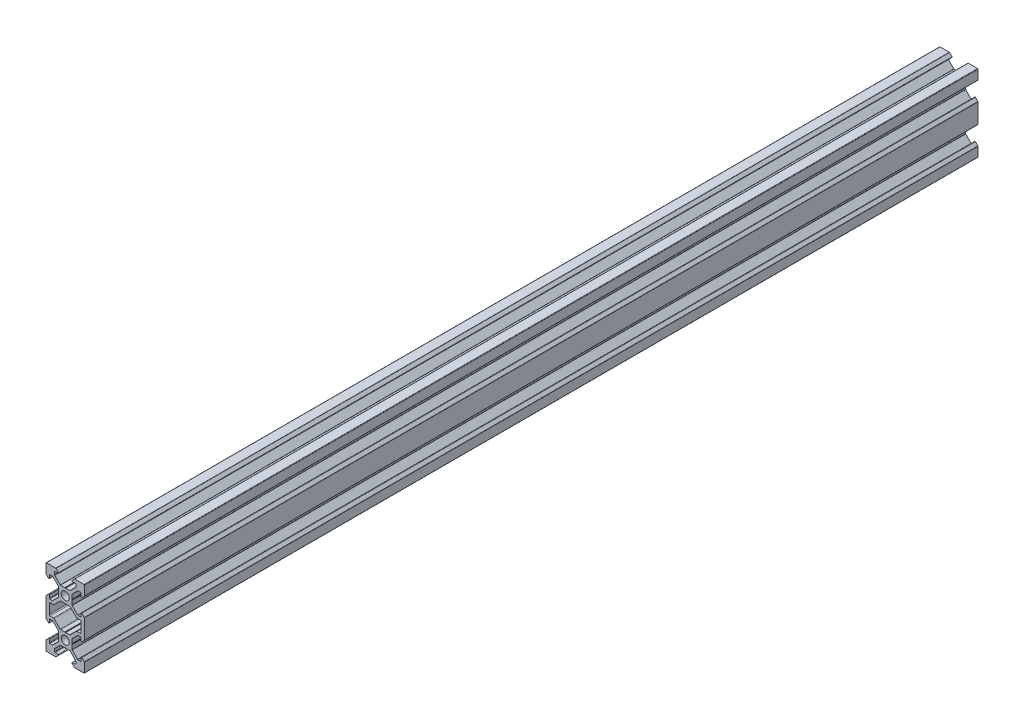
SolidWorks part; units mm, degrees
ref_plane "Front Plane" through (0, 0, 0) normal (0, 0, 1) x (1, 0, 0)
ref_plane "Top Plane" through (0, 0, 0) normal (0, 1, 0) x (1, 0, 0)
ref_plane "Right Plane" through (0, 0, 0) normal (1, 0, 0) x (0, 0, -1)
sketch "Sketch1" plane through (0, 0, 0) normal (0, 0, 1) x (1, 0, 0)
  line L0 (3.5607, 3.5607) -> (10.6317, 10.6317) construction
  line L1 (2.5, -3.5607) -> (-2.5, -3.5607)
  line L2 (3.5607, -2.5) -> (3.5607, 2.5)
  line L3 (2.5, 3.5607) -> (-2.5, 3.5607)
  line L4 (-3.5607, -2.5) -> (-3.5607, 2.5)
  line L5 (3.5607, -3.5607) -> (-3.5607, 3.5607) construction
  line L6 (3.5607, 3.5607) -> (-3.5607, -3.5607) construction
  line L7 (2.5, 3.5607) -> (5.5, 6.5607)
  line L8 (5.5, 6.5607) -> (5.5, 8.2521)
  line L9 (5.5, 8.2521) -> (3.1, 8.2521)
  line L10 (3.1, 8.2521) -> (4.8479, 10)
  line L11 (4.8479, 10) -> (10, 10)
  line L12 (3.5607, 2.5) -> (6.5607, 5.5)
  line L13 (6.5607, 5.5) -> (8.2521, 5.5)
  line L14 (8.2521, 5.5) -> (8.2521, 3.1)
  line L15 (8.2521, 3.1) -> (10, 4.8479)
  line L16 (10, 4.8479) -> (10, 10)
  line L17 (0, -55) -> (0, 55) construction
  line L18 (-3.5607, 3.5607) -> (-10.6317, 10.6317) construction
  line L19 (-10, 4.8479) -> (-10, 10)
  line L20 (-8.2521, 3.1) -> (-10, 4.8479)
  line L21 (-8.2521, 5.5) -> (-8.2521, 3.1)
  line L22 (-6.5607, 5.5) -> (-8.2521, 5.5)
  line L23 (-3.5607, 2.5) -> (-6.5607, 5.5)
  line L24 (-4.8479, 10) -> (-10, 10)
  line L25 (-3.1, 8.2521) -> (-4.8479, 10)
  line L26 (-5.5, 8.2521) -> (-3.1, 8.2521)
  line L27 (-5.5, 6.5607) -> (-5.5, 8.2521)
  line L28 (-2.5, 3.5607) -> (-5.5, 6.5607)
  line L29 (-8.2521, -7) -> (-5.9393, -7)
  line L30 (55, 0) -> (-55, 0) construction
  line L31 (-3.5607, -3.5607) -> (-10.6317, -10.6317) construction
  line L32 (3.5607, -3.5607) -> (10.6317, -10.6317) construction
  line L33 (-2.5, -3.5607) -> (-5.5, -6.5607)
  line L34 (-5.5, -6.5607) -> (-5.9393, -7)
  line L35 (5.5, -6.5607) -> (5.9393, -7)
  line L36 (8.2521, -7) -> (5.9393, -7)
  line L37 (-12.2633, -10) -> (14.5346, -10) construction
  line L38 (-3.5607, -2.5) -> (-6.5607, -5.5)
  line L39 (-6.5607, -5.5) -> (-8.2521, -5.5)
  line L40 (-8.2521, -5.5) -> (-8.2521, -3.1)
  line L41 (-8.2521, -3.1) -> (-10, -4.8479)
  line L42 (-10, -4.8479) -> (-10, -7)
  line L43 (10, -4.8479) -> (10, -7)
  line L44 (8.2521, -3.1) -> (10, -4.8479)
  line L45 (8.2521, -5.5) -> (8.2521, -3.1)
  line L46 (6.5607, -5.5) -> (8.2521, -5.5)
  line L47 (3.5607, -2.5) -> (6.5607, -5.5)
  line L48 (-3.5607, -23.5607) -> (-10.6317, -30.6317) construction
  line L49 (3.5607, -23.5607) -> (-3.5607, -16.4393) construction
  line L50 (3.5607, -16.4393) -> (-3.5607, -23.5607) construction
  line L51 (3.5607, -23.5607) -> (10.6317, -30.6317) construction
  line L52 (2.5, -3.5607) -> (5.5, -6.5607)
  line L53 (2.5, -16.4393) -> (5.5, -13.4393)
  line L54 (3.5607, -17.5) -> (6.5607, -14.5)
  line L55 (6.5607, -14.5) -> (8.2521, -14.5)
  line L56 (8.2521, -14.5) -> (8.2521, -16.9)
  line L57 (8.2521, -16.9) -> (10, -15.1521)
  line L58 (10, -15.1521) -> (10, -13)
  line L59 (-10, -15.1521) -> (-10, -13)
  line L60 (-8.2521, -16.9) -> (-10, -15.1521)
  line L61 (-8.2521, -14.5) -> (-8.2521, -16.9)
  line L62 (-6.5607, -14.5) -> (-8.2521, -14.5)
  line L63 (-3.5607, -17.5) -> (-6.5607, -14.5)
  line L64 (8.2521, -13) -> (5.9393, -13)
  line L65 (5.5, -13.4393) -> (5.9393, -13)
  line L66 (-5.5, -13.4393) -> (-5.9393, -13)
  line L67 (-2.5, -16.4393) -> (-5.5, -13.4393)
  line L68 (-8.2521, -13) -> (-5.9393, -13)
  line L69 (-2.5, -23.5607) -> (-5.5, -26.5607)
  line L70 (-5.5, -26.5607) -> (-5.5, -28.2521)
  line L71 (-5.5, -28.2521) -> (-3.1, -28.2521)
  line L72 (-3.1, -28.2521) -> (-4.8479, -30)
  line L73 (-4.8479, -30) -> (-10, -30)
  line L74 (-3.5607, -22.5) -> (-6.5607, -25.5)
  line L75 (-6.5607, -25.5) -> (-8.2521, -25.5)
  line L76 (-8.2521, -25.5) -> (-8.2521, -23.1)
  line L77 (-8.2521, -23.1) -> (-10, -24.8479)
  line L78 (-10, -24.8479) -> (-10, -30)
  line L79 (10, -24.8479) -> (10, -30)
  line L80 (8.2521, -23.1) -> (10, -24.8479)
  line L81 (8.2521, -25.5) -> (8.2521, -23.1)
  line L82 (6.5607, -25.5) -> (8.2521, -25.5)
  line L83 (3.5607, -22.5) -> (6.5607, -25.5)
  line L84 (4.8479, -30) -> (10, -30)
  line L85 (3.1, -28.2521) -> (4.8479, -30)
  line L86 (5.5, -28.2521) -> (3.1, -28.2521)
  line L87 (5.5, -26.5607) -> (5.5, -28.2521)
  line L88 (2.5, -23.5607) -> (5.5, -26.5607)
  line L89 (-3.5607, -17.5) -> (-3.5607, -22.5)
  line L90 (2.5, -23.5607) -> (-2.5, -23.5607)
  line L91 (3.5607, -17.5) -> (3.5607, -22.5)
  line L92 (2.5, -16.4393) -> (-2.5, -16.4393)
  line L93 (-10, -7) -> (-10, -13)
  line L94 (-8.2521, -13) -> (-8.2521, -7)
  line L95 (8.2521, -13) -> (8.2521, -7)
  line L96 (10, -7) -> (10, -13)
  circle A0 centre (0, 0) radius 2.1
  circle A1 centre (0, -20) radius 2.1
  point P0 (0, 0)
  point P102 (0, -20)
  dimension "D10" = 4.2
  dimension "D11" = 4.2
  dimension "D1" = 1.5
  dimension "D2" = 10
  dimension "D3" = 20
  dimension "D4" = 6.2
  dimension "D5" = 11
  dimension "D6" = 45
  dimension "D7" = 1.5
  dimension "D8" = 10
  dimension "D9" = 5
extrude "Boss-Extrude1" add sketch "Sketch1" along normal blind 465
fillet "Fillet1" radius 0.25 64 edges at (5.5, 6.5607, 232.5) (5.5, 8.2521, 232.5) (3.1, 8.2521, 232.5) (4.8479, 10, 232.5) (10, 10, 232.5) (10, 4.8479, 232.5) (8.2521, 3.1, 232.5) (8.2521, 5.5, 232.5) (6.5607, 5.5, 232.5) (3.5607, 2.5, 232.5) (3.5607, -2.5, 232.5) (6.5607, -5.5, 232.5) (8.2521, -5.5, 232.5) (8.2521, -3.1, 232.5) (10, -4.8479, 232.5) (10, -15.1521, 232.5) (8.2521, -16.9, 232.5) (8.2521, -14.5, 232.5) (6.5607, -14.5, 232.5) (3.5607, -17.5, 232.5) (3.5607, -22.5, 232.5) (6.5607, -25.5, 232.5) (8.2521, -25.5, 232.5) (8.2521, -23.1, 232.5) (10, -24.8479, 232.5) (10, -30, 232.5) (4.8479, -30, 232.5) (3.1, -28.2521, 232.5) (5.5, -28.2521, 232.5) (5.5, -26.5607, 232.5) (2.5, -23.5607, 232.5) (-2.5, -23.5607, 232.5) (-5.5, -26.5607, 232.5) (-5.5, -28.2521, 232.5) (-3.1, -28.2521, 232.5) (-4.8479, -30, 232.5) (-10, -30, 232.5) (-10, -24.8479, 232.5) (-8.2521, -23.1, 232.5) (-8.2521, -25.5, 232.5) (-6.5607, -25.5, 232.5) (-3.5607, -22.5, 232.5) (-3.5607, -17.5, 232.5) (-6.5607, -14.5, 232.5) (-8.2521, -14.5, 232.5) (-8.2521, -16.9, 232.5) (-10, -15.1521, 232.5) (-10, -4.8479, 232.5) (-8.2521, -3.1, 232.5) (-8.2521, -5.5, 232.5) (-6.5607, -5.5, 232.5) (-3.5607, -2.5, 232.5) (-3.5607, 2.5, 232.5) (-6.5607, 5.5, 232.5) (-8.2521, 5.5, 232.5) (-8.2521, 3.1, 232.5) (-10, 4.8479, 232.5) (-10, 10, 232.5) (-4.8479, 10, 232.5) (-5.5, 8.2521, 232.5) (-5.5, 6.5607, 232.5) (-2.5, 3.5607, 232.5) (2.5, 3.5607, 232.5) (-3.1, 8.2521, 232.5)
fillet "Fillet2" radius 0.5 12 edges at (-5.9393, -7, 232.5) (-8.2521, -7, 232.5) (-8.2521, -13, 232.5) (-5.9393, -13, 232.5) (-2.5, -16.4393, 232.5) (2.5, -16.4393, 232.5) (8.2521, -7, 232.5) (5.9393, -7, 232.5) (2.5, -3.5607, 232.5) (-2.5, -3.5607, 232.5) (5.9393, -13, 232.5) (8.2521, -13, 232.5)
sketch "Sketch2" plane through (0, 0, 465) normal (0, 0, 1) x (1, 0, 0)
  line L4 (0, 3.5607) -> (0, 3.1447) construction
  line L5 (2.3964, 3.5607) -> (-2.3964, 3.5607) construction
  line L6 (0, 3.399) -> (-0.2423, 3.5607)
  line L7 (0, 3.399) -> (0.2423, 3.5607)
  line L8 (-0.2423, 3.5607) -> (0.2423, 3.5607)
  line L9 (55, 0) -> (-55, 0) construction
  line L10 (0, -3.5607) -> (0, -3.1447) construction
  line L11 (0, -3.399) -> (0.2423, -3.5607)
  line L12 (0, -3.399) -> (-0.2423, -3.5607)
  line L13 (-0.2423, -3.5607) -> (0.2423, -3.5607)
  line L14 (0, 0) -> (-4.0856, 4.0856) construction
  line L15 (-8.2521, -10) -> (4.1581, -10) construction
  line L16 (-8.2521, -7.5) -> (-8.2521, -12.5) construction
  line L17 (3.5607, 0) -> (3.1447, 0) construction
  line L18 (3.5607, 0.2423) -> (3.5607, -0.2423)
  line L19 (3.399, 0) -> (3.5607, 0.2423)
  line L20 (3.399, 0) -> (3.5607, -0.2423)
  line L21 (-3.5607, 0) -> (-3.1447, 0) construction
  line L22 (-3.5607, 0.2423) -> (-3.5607, -0.2423)
  line L23 (-3.399, 0) -> (-3.5607, -0.2423)
  line L24 (-3.399, 0) -> (-3.5607, 0.2423)
  line L25 (-3.5607, -20) -> (-3.1447, -20) construction
  line L26 (3.5607, -20) -> (3.1447, -20) construction
  line L27 (0, -20) -> (-4.0856, -24.0856) construction
  line L28 (0, -16.4393) -> (0, -16.8553) construction
  line L29 (0, -23.5607) -> (0, -23.1447) construction
  line L30 (-3.399, -20) -> (-3.5607, -20.2423)
  line L31 (-3.399, -20) -> (-3.5607, -19.7577)
  line L32 (-3.5607, -20.2423) -> (-3.5607, -19.7577)
  line L33 (3.399, -20) -> (3.5607, -19.7577)
  line L34 (3.399, -20) -> (3.5607, -20.2423)
  line L35 (3.5607, -20.2423) -> (3.5607, -19.7577)
  line L36 (-0.2423, -16.4393) -> (0.2423, -16.4393)
  line L37 (0, -16.601) -> (-0.2423, -16.4393)
  line L38 (0, -16.601) -> (0.2423, -16.4393)
  line L39 (-0.2423, -23.5607) -> (0.2423, -23.5607)
  line L40 (0, -23.399) -> (0.2423, -23.5607)
  line L41 (0, -23.399) -> (-0.2423, -23.5607)
extrude "Cut-Extrude1" cut sketch "Sketch2" against normal through all
